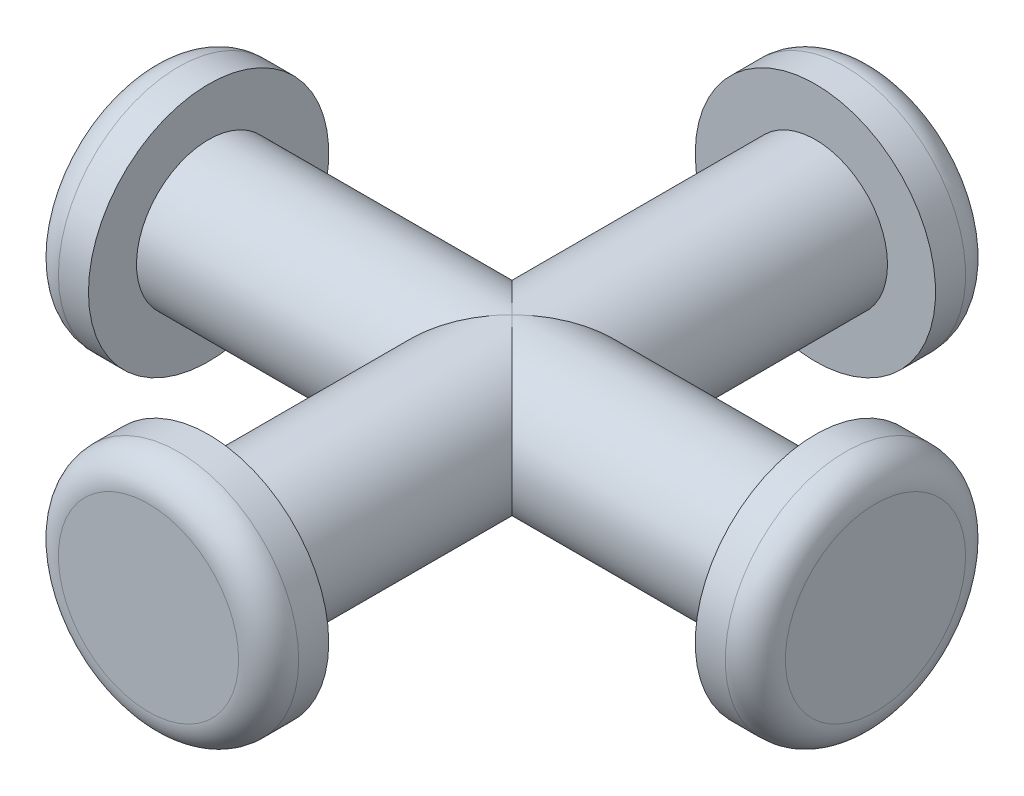
SolidWorks part; units mm, degrees
ref_plane "Plan de face" through (0, 0, 0) normal (0, 0, 1) x (1, 0, 0)
ref_plane "Plan de dessus" through (0, 0, 0) normal (0, 1, 0) x (1, 0, 0)
ref_plane "Plan de droite" through (0, 0, 0) normal (1, 0, 0) x (0, 0, -1)
sketch "Esquisse1" plane through (0, 0, 0) normal (0, 0, 1) x (1, 0, 0)
  circle A0 centre (0, 0) radius 2.4
  dimension "D1" = 4.8
extrude "Boss.-Extru.1" add sketch "Esquisse1" along normal mid plane 20.2 contours A0
sketch "Esquisse3" plane through (0, 0, 0) normal (1, 0, 0) x (0, 0, -1)
  circle A0 centre (0, 0) radius 2.4
  dimension "D1" = 4.8
extrude "Boss.-Extru.2" add sketch "Esquisse3" along normal mid plane 20.2
sketch "Esquisse4" plane through (10.1, 0, 0) normal (1, 0, 0) x (0, 0, -1)
  circle A0 centre (0, 0) radius 4
  dimension "D1" = 8
extrude "Boss.-Extru.3" add sketch "Esquisse4" along normal blind 2 contours A0
sketch "Esquisse5" plane through (-10.1, 0, 0) normal (-1, 0, 0) x (0, 0, 1)
  circle A0 centre (0, 0) radius 4
  dimension "D1" = 8
extrude "Boss.-Extru.4" add sketch "Esquisse5" along normal blind 2
sketch "Esquisse6" plane through (0, 0, 10.1) normal (0, 0, 1) x (1, 0, 0)
  circle A0 centre (0, 0) radius 4
  dimension "D1" = 8
extrude "Boss.-Extru.5" add sketch "Esquisse6" along normal blind 2
sketch "Esquisse7" plane through (0, 0, -10.1) normal (0, 0, -1) x (-1, 0, 0)
  circle A0 centre (0, 0) radius 4
  dimension "D1" = 8
extrude "Boss.-Extru.6" add sketch "Esquisse7" along normal blind 2 contours A0
fillet "Congé1" radius 1 4 edges at (-12.1, 0, 4) (-4, 0, -12.1) (12.1, 0, -4) (4, 0, 12.1)
